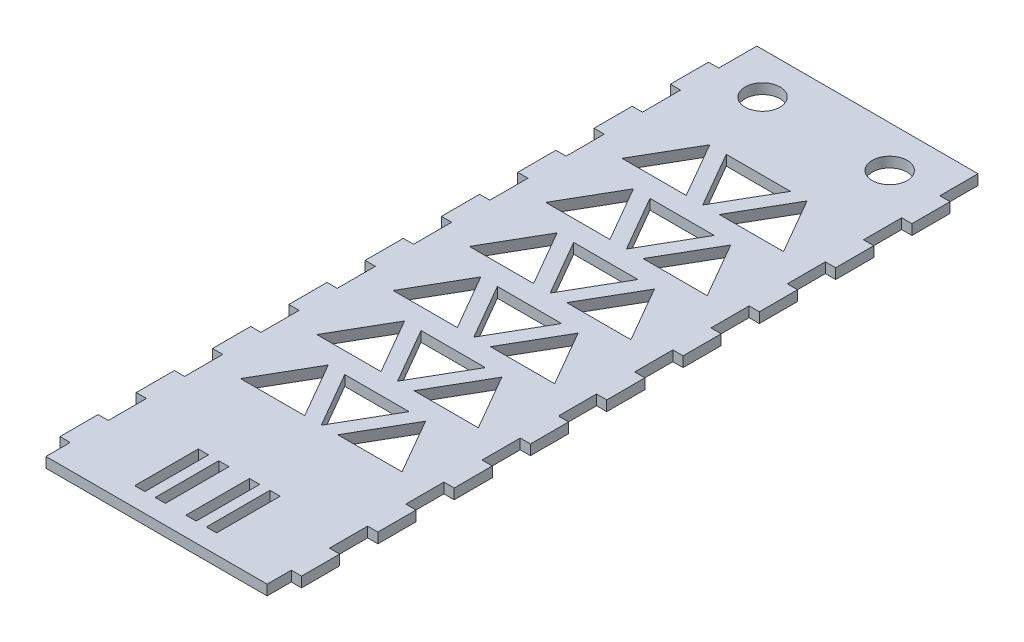
SolidWorks part; units mm, degrees
ref_plane "Front Plane" through (0, 0, 0) normal (0, 0, 1) x (1, 0, 0)
ref_plane "Top Plane" through (0, 0, 0) normal (0, 1, 0) x (1, 0, 0)
ref_plane "Right Plane" through (0, 0, 0) normal (1, 0, 0) x (0, 0, -1)
sketch "Sketch1" plane through (0, 0, 0) normal (0, 1, 0) x (1, 0, 0)
  line L1 (-38, 111.8034) -> (38, 111.8034)
  line L2 (-38, 111.8034) -> (-38, -111.8034)
  line L3 (-38, -111.8034) -> (38, -111.8034)
  line L4 (38, 111.8034) -> (38, -111.8034)
  line L5 (-38, 111.8034) -> (38, -111.8034) construction
  line L6 (-38, -111.8034) -> (38, 111.8034) construction
  point P0 (0, 0)
  dimension "D1" = 223.6068
  dimension "D2" = 76
extrude "Boss-Extrude1" add sketch "Sketch1" along normal mid plane 3.22
sketch "Sketch2" plane through (0, 1.61, 0) normal (0, 1, 0) x (1, 0, 0)
  line L0 (38, 111.8034) -> (-38, 111.8034) construction
  line L1 (38, 99.8034) -> (34.78, 99.8034)
  line L2 (38, 99.8034) -> (38, 111.8034)
  line L3 (38, 111.8034) -> (34.78, 111.8034)
  line L4 (34.78, 99.8034) -> (34.78, 111.8034)
  line L5 (38, -111.8034) -> (38, 111.8034) construction
  point P7 (34.78, 111.8034)
  point P10 (34.948, 99.8046)
  dimension "D1" = 12
  dimension "D2" = 3.22
extrude "Cut-Extrude1" cut sketch "Sketch2" against normal blind 3.22
pattern_linear "LPattern1" count 10 spacing 24 along (0, 0, 1) of "Cut-Extrude1"
mirror "Mirror1" about plane through (0, 0, 0) normal (1, 0, 0) of "LPattern1", "Cut-Extrude1"
ref_plane "Plane1" through (0, 46.0094, -23.0047) normal (0, 0.8944, -0.4472) x (-1, 0, 0)
sketch "Sketch4" plane through (0, -1.61, 0) normal (0, -1, 0) x (1, 0, 0)
  line L1 (20, -98.8034) -> (-20, -98.8034) construction
  line L2 (0, -1.771) -> (0, 1.771) construction
  line L3 (34.78, -111.8034) -> (-34.78, -111.8034) construction
  circle A0 centre (-20, -98.8034) radius 5.5
  circle A1 centre (20, -98.8034) radius 5.5
  point P4 (0, -98.8034)
  dimension "D1" = 11
  dimension "D2" = 40
  dimension "D3" = 13
extrude "Cut-Extrude2" cut sketch "Sketch4" against normal blind 10
sketch "Sketch7" plane through (0, -1.61, 0) normal (0, -1, 0) x (1, 0, 0)
  line L0 (-9.66, 105.8034) -> (-6.44, 105.8034) construction
  line L1 (-12.88, 85.8034) -> (-9.66, 85.8034)
  line L2 (-12.88, 85.8034) -> (-12.88, 105.8034)
  line L3 (-12.88, 105.8034) -> (-9.66, 105.8034)
  line L4 (-9.66, 85.8034) -> (-9.66, 105.8034)
  line L5 (-12.88, 85.8034) -> (-9.66, 105.8034) construction
  line L6 (-12.88, 105.8034) -> (-9.66, 85.8034) construction
  line L7 (-6.44, 85.8034) -> (-3.22, 85.8034)
  line L8 (-6.44, 85.8034) -> (-6.44, 105.8034)
  line L9 (-6.44, 105.8034) -> (-3.22, 105.8034)
  line L10 (-3.22, 85.8034) -> (-3.22, 105.8034)
  line L11 (-6.44, 85.8034) -> (-3.22, 105.8034) construction
  line L12 (-6.44, 105.8034) -> (-3.22, 85.8034) construction
  line L13 (3.22, 85.8034) -> (6.44, 85.8034)
  line L14 (3.22, 85.8034) -> (3.22, 105.8034)
  line L15 (3.22, 105.8034) -> (6.44, 105.8034)
  line L16 (6.44, 85.8034) -> (6.44, 105.8034)
  line L17 (3.22, 85.8034) -> (6.44, 105.8034) construction
  line L18 (3.22, 105.8034) -> (6.44, 85.8034) construction
  line L19 (9.66, 85.8034) -> (12.88, 85.8034)
  line L20 (9.66, 85.8034) -> (9.66, 105.8034)
  line L21 (9.66, 105.8034) -> (12.88, 105.8034)
  line L22 (12.88, 85.8034) -> (12.88, 105.8034)
  line L23 (9.66, 85.8034) -> (12.88, 105.8034) construction
  line L24 (9.66, 105.8034) -> (12.88, 85.8034) construction
  line L26 (6.44, 105.8034) -> (9.66, 105.8034) construction
  line L27 (-3.22, 95.8034) -> (3.22, 95.8034) construction
  line L28 (-34.78, 111.8034) -> (34.78, 111.8034) construction
  point P0 (-11.27, 95.8034)
  point P5 (-4.83, 95.8034)
  point P10 (4.83, 95.8034)
  point P15 (11.27, 95.8034)
  point P23 (0, 95.8034)
  dimension "D2" = 3.22
  dimension "D1" = 20
  dimension "D3" = 3.22
  dimension "D4" = 16
extrude "Cut-Extrude5" cut sketch "Sketch7" against normal up to next
sketch "Sketch8" plane through (0, 1.61, 0) normal (0, 1, 0) x (1, 0, 0)
  line L0 (-5.2, 60) -> (-15.3036, 77.5)
  line L1 (-15.3036, 77.5) -> (-25.4073, 60)
  line L2 (-25.4073, 60) -> (-5.2, 60)
  line L5 (-10.1036, 77.5) -> (10.1036, 77.5)
  line L6 (0, 60) -> (-10.1036, 77.5)
  line L7 (10.1036, 77.5) -> (0, 60)
  line L8 (-15.3036, 77.5) -> (-10.1036, 77.5) construction
  line L9 (0, 60) -> (0, 77.5) construction
  line L10 (15.3036, 77.5) -> (25.4073, 60)
  line L11 (5.2, 60) -> (15.3036, 77.5)
  line L12 (25.4073, 60) -> (5.2, 60)
  dimension "D1" = 17.5
  dimension "D2" = 5.2
  dimension "D3" = 60
extrude "Cut-Extrude7" cut sketch "Sketch8" against normal up to next (3.22 mm away)
pattern_linear "LPattern2" count 6 spacing 24 along (0, 0, 1) of "Cut-Extrude7"
equation "\"D3@LPattern1\"=2*\"D1@Sketch2\""
equation "\"D1@Plane1\"= atn ( 10 / 20 )"
equation "\"D3@Sketch7\"  = \"D2@Sketch7\""
